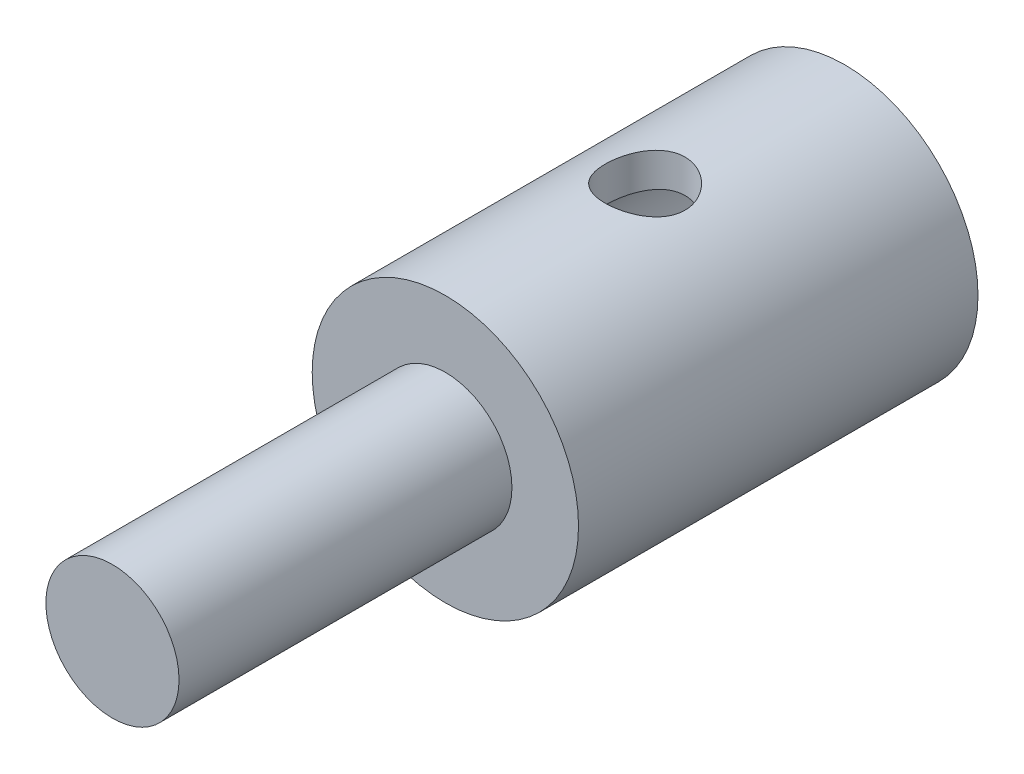
SolidWorks part; units mm, degrees
material "Laiton"
ref_plane "Plan de face" through (0, 0, 0) normal (0, 0, 1) x (1, 0, 0)
ref_plane "Plan de dessus" through (0, 0, 0) normal (0, 1, 0) x (1, 0, 0)
ref_plane "Plan de droite" through (0, 0, 0) normal (1, 0, 0) x (0, 0, -1)
sketch "Esquisse1" plane through (0, 0, 0) normal (1, 0, 0) x (0, 0, -1)
  line L0 (-5.5, 0) -> (5.5, 0) construction
  line L1 (-5.5, 0) -> (-5.5, 1)
  line L2 (-5.5, 1) -> (-0.5, 1)
  line L3 (-0.5, 1) -> (-0.5, 2)
  line L4 (-0.5, 2) -> (5.5, 2)
  line L5 (5.5, 2) -> (5.5, 1.5)
  line L6 (5.5, 1.5) -> (1.5, 1.5)
  line L7 (1.5, 1.5) -> (1.5, 0)
  line L8 (-5.5, 0) -> (1.5, 0)
  dimension "D1" = 11
  dimension "D2" = 1.5
  dimension "D3" = 6
  dimension "D4" = 2
  dimension "D5" = 1
  dimension "D6" = 4
revolve "Révolution1" add sketch "Esquisse1" angle 360 about L0
sketch "Esquisse2" plane through (0, 0, 0) normal (0, 1, 0) x (1, 0, 0)
  line L0 (-2, 5.5) -> (2, -0.5) construction
  circle A0 centre (0, 2.5) radius 0.6
  dimension "D1" = 1.2
extrude "Enlèv. mat.-Extru.1" cut sketch "Esquisse2" against normal through all and the other way through all
